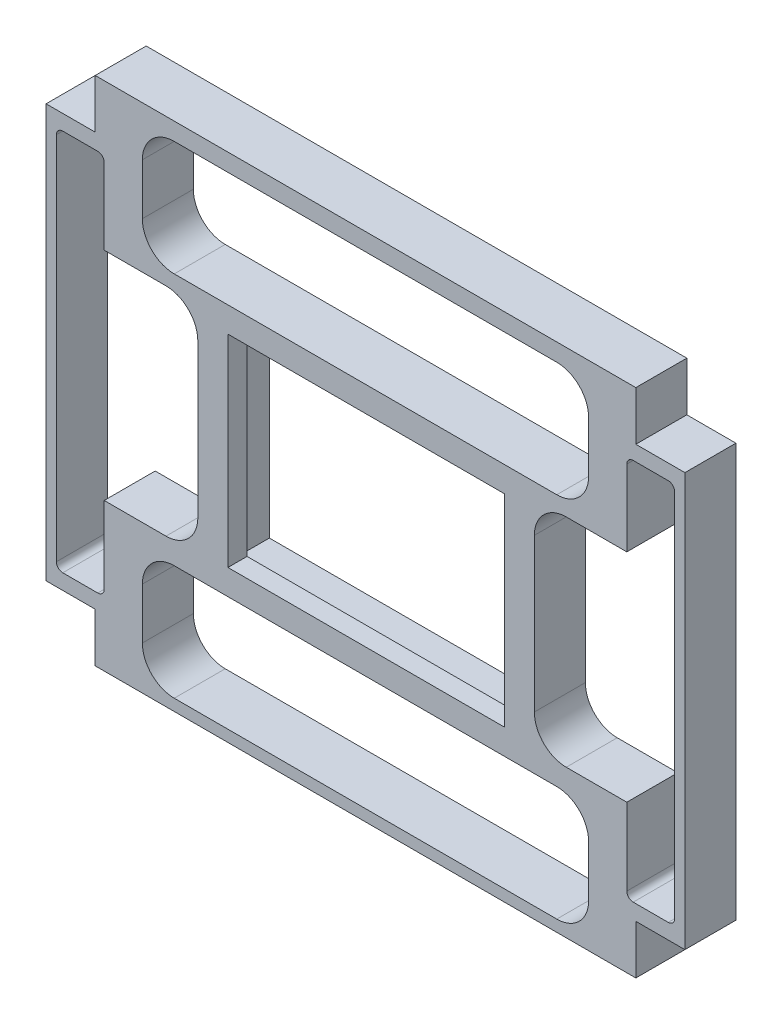
SolidWorks part; units mm, degrees
ref_plane "Plan de face" through (0, 0, 0) normal (0, 0, 1) x (1, 0, 0)
ref_plane "Plan de dessus" through (0, 0, 0) normal (0, 1, 0) x (1, 0, 0)
ref_plane "Plan de droite" through (0, 0, 0) normal (1, 0, 0) x (0, 0, -1)
sketch "Esquisse1" plane through (0, 0, 0) normal (0, 0, 1) x (1, 0, 0)
  line L4 (-47.9586, -0.2167) -> (52.2414, -0.2167) construction
  line L5 (-40.2586, 39.8833) -> (44.5414, 39.8833)
  line L6 (-47.9586, 32.1833) -> (-47.9586, -32.6167)
  line L7 (-40.2586, -40.3167) -> (44.5414, -40.3167)
  line L8 (52.2414, 32.1833) -> (52.2414, -32.6167)
  line L11 (-47.9586, 32.1833) -> (-40.2586, 32.1833)
  line L12 (-40.2586, 39.8833) -> (-40.2586, 32.1833)
  line L13 (2.1414, 39.8833) -> (2.1414, -40.3167) construction
  line L14 (44.5414, 39.8833) -> (44.5414, 32.1833)
  line L15 (52.2414, 32.1833) -> (44.5414, 32.1833)
  line L16 (52.2414, -32.6167) -> (44.5414, -32.6167)
  line L17 (44.5414, -40.3167) -> (44.5414, -32.6167)
  line L18 (-40.2586, -40.3167) -> (-40.2586, -32.6167)
  line L19 (-47.9586, -32.6167) -> (-40.2586, -32.6167)
  line L24 (-20.9336, 16.8583) -> (25.2164, 16.8583)
  line L25 (-20.9336, 16.8583) -> (-20.9336, -17.2917)
  line L26 (-20.9336, -17.2917) -> (25.2164, -17.2917)
  line L27 (25.2164, 16.8583) -> (25.2164, -17.2917)
  point P1 (0, 0)
  point P6 (2.1414, -0.2167)
  dimension "D1" = 46.15
  dimension "D2" = 34.15
  dimension "D3" = 17.075
  dimension "D4" = 23.075
  dimension "D5" = 7.7
  dimension "D6" = 7.7
  dimension "D7" = 84.8
  dimension "D8" = 64.8
extrude "Boss.-Extru.1" add sketch "Esquisse1" along normal blind 5
sketch "Esquisse2" plane through (0, 0, 5) normal (0, 0, 1) x (1, 0, 0)
  line L0 (-47.9586, 32.1833) -> (-40.2586, 32.1833)
  line L1 (-40.2586, 32.1833) -> (-40.2586, 39.8833)
  line L2 (-40.2586, 39.8833) -> (44.5414, 39.8833)
  line L3 (44.5414, 39.8833) -> (44.5414, 32.1833)
  line L4 (44.5414, 32.1833) -> (52.2414, 32.1833)
  line L5 (52.2414, 32.1833) -> (52.2414, -32.6167)
  line L6 (52.2414, -32.6167) -> (44.5414, -32.6167)
  line L7 (44.5414, -32.6167) -> (44.5414, -40.3167)
  line L8 (44.5414, -40.3167) -> (-40.2586, -40.3167)
  line L9 (-40.2586, -40.3167) -> (-40.2586, -32.6167)
  line L10 (-40.2586, -32.6167) -> (-47.9586, -32.6167)
  line L11 (-47.9586, -32.6167) -> (-47.9586, 32.1833)
extrude "Boss.-Extru.2" add sketch "Esquisse2" along normal blind 3
sketch "Esquisse6" plane through (0, 0, 0) normal (0, 0, -1) x (-1, 0, 0)
  line L0 (-2.1414, 39.8833) -> (-2.1414, -40.3167) construction
  line L1 (-49.6289, 29.7833) -> (-44.1289, 29.7833)
  line L2 (-50.6289, 28.7833) -> (-50.6289, -29.2167)
  line L3 (-49.6289, -30.2167) -> (-44.1289, -30.2167)
  line L4 (-43.1289, 28.7833) -> (-43.1289, -29.2167)
  line L5 (-44.5414, 39.8833) -> (40.2586, 39.8833) construction
  line L6 (40.2586, -40.3167) -> (-44.5414, -40.3167) construction
  line L10 (-52.2414, 32.1833) -> (-41.5164, 32.1833) construction
  line L13 (-50.6289, -0.2167) -> (-43.1289, -0.2167) construction
  line L14 (45.3461, -30.2167) -> (39.8461, -30.2167)
  line L15 (38.8461, 28.7833) -> (38.8461, -29.2167)
  line L16 (45.3461, 29.7833) -> (39.8461, 29.7833)
  line L17 (46.3461, 28.7833) -> (46.3461, -29.2167)
  arc A0 (-49.6289, -30.2167) -> (-50.6289, -29.2167) centre (-49.6289, -29.2167) cw
  arc A1 (-44.1289, -30.2167) -> (-43.1289, -29.2167) centre (-44.1289, -29.2167) ccw
  arc A2 (-44.1289, 29.7833) -> (-43.1289, 28.7833) centre (-44.1289, 28.7833) cw
  arc A3 (-49.6289, 29.7833) -> (-50.6289, 28.7833) centre (-49.6289, 28.7833) ccw
  arc A4 (39.8461, -30.2167) -> (38.8461, -29.2167) centre (39.8461, -29.2167) cw
  arc A5 (39.8461, 29.7833) -> (38.8461, 28.7833) centre (39.8461, 28.7833) ccw
  arc A6 (45.3461, -30.2167) -> (46.3461, -29.2167) centre (45.3461, -29.2167) ccw
  arc A7 (45.3461, 29.7833) -> (46.3461, 28.7833) centre (45.3461, 28.7833) cw
  point P16 (-50.6289, -0.2167)
  point P23 (-46.8789, -0.2167)
  point P26 (-50.6289, -30.2167)
  point P31 (-43.1289, 29.7833)
  point P34 (-50.6289, 29.7833)
  dimension "D3" = 1
  dimension "D1" = 7.5
  dimension "D2" = 60
extrude "Enlèv. mat.-Extru.4" cut sketch "Esquisse6" against normal through all
sketch "Esquisse7" plane through (0, 0, 5) normal (0, 0, -1) x (-1, 0, 0)
  line L1 (-23.9114, 15.1583) -> (19.4386, 15.1583)
  line L2 (-23.9114, 15.1583) -> (-23.9114, -16.5417)
  line L3 (-23.9114, -16.5417) -> (19.4386, -16.5417)
  line L4 (19.4386, 15.1583) -> (19.4386, -16.5417)
  line L6 (-25.1414, 16.7833) -> (-23.9114, 15.1583) construction
  point P12 (-25.2164, 16.8583)
  point P17 (0, 0)
  point P18 (0, 0)
extrude "Enlèv. mat.-Extru.5" cut sketch "Esquisse7" against normal blind 7
sketch "Esquisse8" plane through (0, 0, 0) normal (0, 0, -1) x (-1, 0, 0)
  line L0 (-23.9114, -0.6917) -> (19.4386, -0.6917) construction
  line L1 (-32.1414, 37.1279) -> (27.8586, 37.1279)
  line L2 (-37.1414, 32.1279) -> (-37.1414, 24.1279)
  line L3 (-32.1414, 19.1279) -> (27.8586, 19.1279)
  line L4 (32.8586, 32.1279) -> (32.8586, 24.1279)
  line L5 (-23.9114, 15.1583) -> (-23.9114, -16.5417) construction
  line L6 (19.4386, -16.5417) -> (19.4386, 15.1583) construction
  line L9 (-32.1414, -20.5112) -> (27.8586, -20.5112)
  line L10 (32.8586, -33.5112) -> (32.8586, -25.5112)
  line L11 (-32.1414, -38.5112) -> (27.8586, -38.5112)
  line L12 (-37.1414, -33.5112) -> (-37.1414, -25.5112)
  line L13 (-2.2364, 15.1583) -> (-2.2364, -16.5417) construction
  line L14 (19.4386, 15.1583) -> (-23.9114, 15.1583) construction
  line L15 (-23.9114, -16.5417) -> (19.4386, -16.5417) construction
  line L16 (-25.2164, 16.8583) -> (-69.6385, 16.8583) construction
  line L17 (-43.1289, 16.8583) -> (-33.6289, 16.8583)
  line L19 (-43.1289, -29.2167) -> (-43.1289, 28.7833) construction
  line L20 (-28.6289, 11.8583) -> (-28.6289, -12.1417)
  line L21 (-33.6289, -17.1417) -> (-45.647, -17.1417)
  line L22 (-45.647, -17.1417) -> (-45.647, 16.8583)
  line L23 (-45.647, 16.8583) -> (-43.1289, 16.8583)
  line L24 (41.1742, -17.1417) -> (41.1742, 16.8583)
  line L25 (29.1561, -17.1417) -> (41.1742, -17.1417)
  line L26 (24.1561, 11.8583) -> (24.1561, -12.1417)
  line L27 (38.6561, 16.8583) -> (29.1561, 16.8583)
  line L28 (41.1742, 16.8583) -> (38.6561, 16.8583)
  arc A0 (32.8586, -33.5112) -> (27.8586, -38.5112) centre (27.8586, -33.5112) cw
  arc A1 (32.8586, -25.5112) -> (27.8586, -20.5112) centre (27.8586, -25.5112) ccw
  arc A2 (-37.1414, -33.5112) -> (-32.1414, -38.5112) centre (-32.1414, -33.5112) ccw
  arc A3 (-32.1414, -20.5112) -> (-37.1414, -25.5112) centre (-32.1414, -25.5112) ccw
  arc A4 (-28.6289, 11.8583) -> (-33.6289, 16.8583) centre (-33.6289, 11.8583) ccw
  arc A5 (-33.6289, -17.1417) -> (-28.6289, -12.1417) centre (-33.6289, -12.1417) ccw
  arc A6 (29.1561, -17.1417) -> (24.1561, -12.1417) centre (29.1561, -12.1417) cw
  arc A7 (29.1561, 16.8583) -> (24.1561, 11.8583) centre (29.1561, 11.8583) ccw
  arc A8 (32.8586, 24.1279) -> (27.8586, 19.1279) centre (27.8586, 24.1279) cw
  arc A9 (-37.1414, 24.1279) -> (-32.1414, 19.1279) centre (-32.1414, 24.1279) ccw
  arc A10 (27.8586, 37.1279) -> (32.8586, 32.1279) centre (27.8586, 32.1279) cw
  arc A11 (-32.1414, 37.1279) -> (-37.1414, 32.1279) centre (-32.1414, 32.1279) ccw
  point P37 (32.8586, -38.5112)
  point P40 (32.8586, -20.5112)
  point P43 (-37.1414, -38.5112)
  point P46 (-37.1414, -20.5112)
  point P49 (-28.6289, 16.8583)
  point P52 (-28.6289, -17.1417)
  point P55 (24.1561, -17.1417)
  point P58 (24.1561, 16.8583)
  point P61 (32.8586, 19.1279)
  point P64 (-37.1414, 19.1279)
  point P67 (32.8586, 37.1279)
  point P70 (-37.1414, 37.1279)
  dimension "D5" = 5
  dimension "D1" = 70
  dimension "D2" = 18
  dimension "D3" = 14.5
  dimension "D4" = 34
extrude "Enlèv. mat.-Extru.6" cut sketch "Esquisse8" against normal through all
